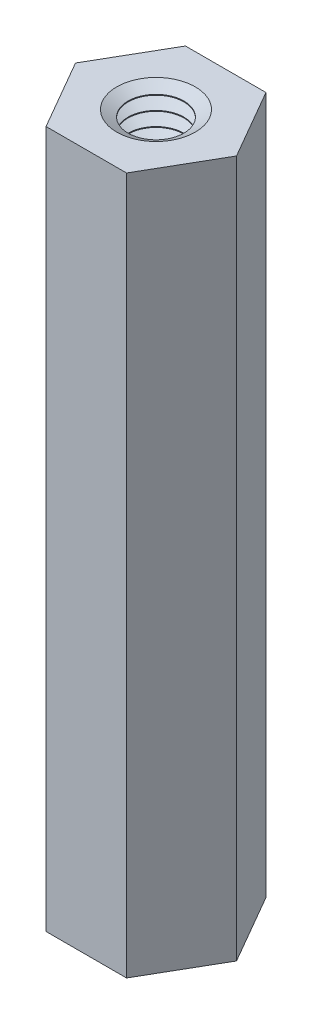
SolidWorks part; units mm, degrees
material "ABS"
ref_plane "Front Plane" through (0, 0, 0) normal (0, 0, 1) x (1, 0, 0)
ref_plane "Top Plane" through (0, 0, 0) normal (0, 1, 0) x (1, 0, 0)
ref_plane "Right Plane" through (0, 0, 0) normal (1, 0, 0) x (0, 0, -1)
sketch "Sketch1" plane through (0, 0, 0) normal (0, 1, 0) x (1, 0, 0)
  line L1 (2.3094, 0) -> (1.1547, 2)
  line L2 (1.1547, 2) -> (-1.1547, 2)
  line L3 (-1.1547, 2) -> (-2.3094, 0)
  line L4 (-2.3094, 0) -> (-1.1547, -2)
  line L5 (-1.1547, -2) -> (1.1547, -2)
  line L6 (1.1547, -2) -> (2.3094, 0)
  circle A0 centre (0, 0) radius 2 construction
  dimension "D1" = 4
extrude "Boss-Extrude1" add sketch "Sketch1" along normal mid plane 20
sketch "Sketch3" plane through (0, -10, 0) normal (0, -1, 0) x (1, 0, 0)
  circle A0 centre (0, 0) radius 0.8
  dimension "D1" = 1.6
extrude "Cut-Extrude1" cut sketch "Sketch3" against normal up to surface (20 mm away) up to face at (0, 10, 0)
sketch "Sketch5" plane through (0, 0, 0) normal (0, 0, 1) x (1, 0, 0)
  line L0 (0, 0) -> (0, -10) construction
  line L1 (0.38, -10) -> (0.78, -10) construction
  line L2 (0.78, -10) -> (1.1264, -10) construction
  line L3 (0.78, -10.2) -> (0.78, -9.8) construction
  line L4 (0.38, -9.8) -> (0.38, -10.2)
  line L5 (0.38, -9.8) -> (0.78, -9.8)
  line L6 (0.78, -9.8) -> (1.1264, -10)
  line L7 (1.1264, -10) -> (0.78, -10.2)
  line L8 (0.78, -10.2) -> (0.38, -10.2)
  line L12 (-0.8, -10) -> (0.8, -10) construction
  line L13 (0, -10) -> (0.38, -10) construction
  point P1 (0.7841, -10)
  point P7 (0, 0)
  point P14 (0.2358, -10)
  dimension "D1" = 60
  dimension "D2" = 0.4
  dimension "D3" = 0.38
revolve "Cut-Revolve3" cut sketch "Sketch5" angle 360 about L0
pattern_linear "LPattern3" count 15 spacing 0.4 along (0, 1, 0) of "Cut-Revolve3"
mirror "Mirror2" about plane through (0, 0, 0) normal (0, 1, 0) of "LPattern3", "Cut-Revolve3"
